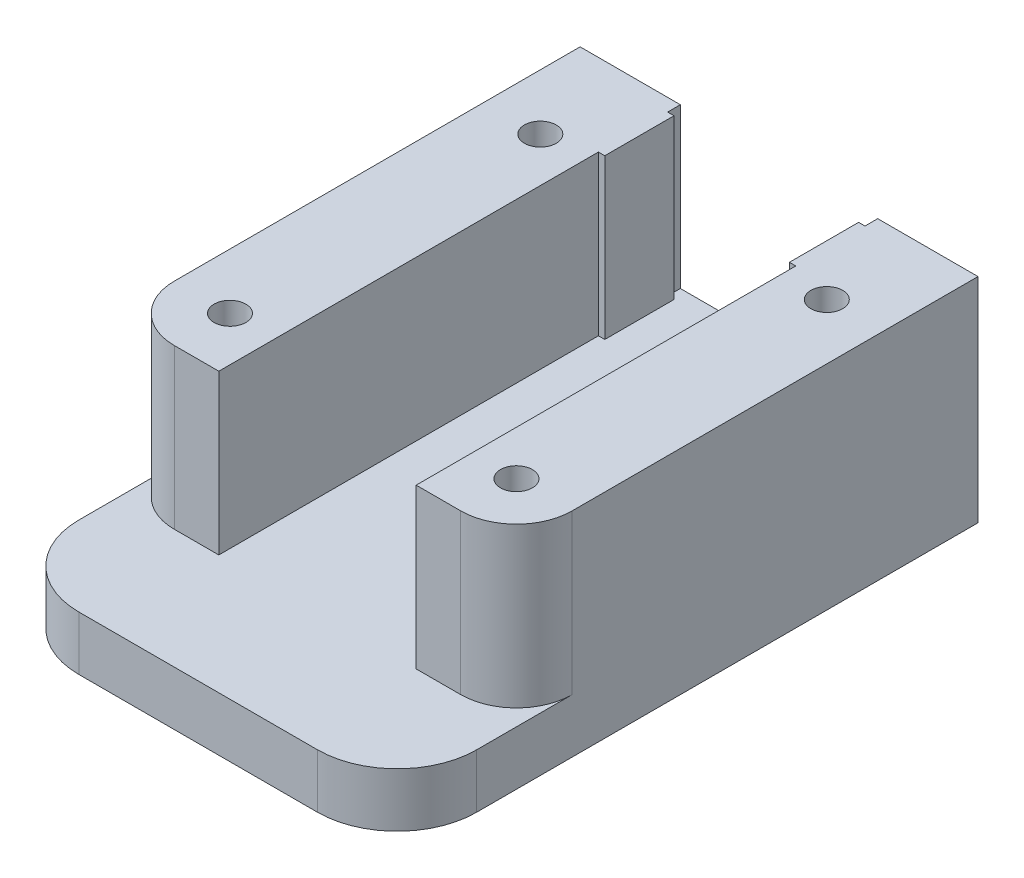
SolidWorks part; units mm, degrees
ref_plane "Front Plane" through (0, 0, 0) normal (0, 0, 1) x (1, 0, 0)
ref_plane "Top Plane" through (0, 0, 0) normal (0, 1, 0) x (1, 0, 0)
ref_plane "Right Plane" through (0, 0, 0) normal (1, 0, 0) x (0, 0, -1)
sketch "Sketch1" plane through (0, 0, 0) normal (0, 1, 0) x (1, 0, 0)
  line L1 (-15, -12.5) -> (15, -12.5)
  line L2 (-15, -12.5) -> (-15, 0)
  line L3 (-15, 0) -> (15, 0)
  line L4 (15, -12.5) -> (15, 0)
  line L5 (-15, -12.5) -> (15, 0) construction
  line L6 (-15, 0) -> (15, -12.5) construction
  point P0 (0, -6.25)
  dimension "D1" = 30
  dimension "D2" = 12.5
extrude "Boss-Extrude1" add sketch "Sketch1" along normal blind 1.6
sketch "Sketch2" plane through (0, 1.6, 0) normal (0, 1, 0) x (1, 0, 0)
  line L0 (15, 0) -> (-15, 0) construction
  line L1 (-12.5, -36.5) -> (12.5, -36.5)
  line L2 (-12.5, -36.5) -> (-12.5, 0)
  line L3 (-12.5, 0) -> (12.5, 0)
  line L4 (12.5, -36.5) -> (12.5, 0)
  line L5 (-12.5, -36.5) -> (12.5, 0) construction
  line L6 (-12.5, 0) -> (12.5, -36.5) construction
  line L7 (0, 0) -> (0, -18.25) construction
  line L8 (-15, -12.5) -> (15, -12.5) construction
  point P0 (0, -18.25)
  dimension "D1" = 25
  dimension "D2" = 24
extrude "Boss-Extrude2" add sketch "Sketch2" along normal blind 3.4
sketch "Sketch3" plane through (0, 5, 0) normal (0, 1, 0) x (1, 0, 0)
  line L1 (-12.5, 0) -> (-6.2, 0)
  line L2 (-12.5, 0) -> (-12.5, -30)
  line L3 (-12.5, -30) -> (-6.2, -30)
  line L4 (-6.2, 0) -> (-6.2, -30)
  line L6 (12.5, 0) -> (6.2, 0)
  line L7 (12.5, 0) -> (12.5, -30)
  line L8 (12.5, -30) -> (6.2, -30)
  line L9 (6.2, 0) -> (6.2, -30)
  dimension "D1" = 12.4
  dimension "D2" = 30
extrude "Boss-Extrude3" add sketch "Sketch3" along normal blind 10
fillet "Fillet1" radius 5 2 edges at (12.5, 3.3, 36.5) (-12.5, 3.3, 36.5)
sketch "Sketch4" plane through (0, 15, 0) normal (0, 1, 0) x (1, 0, 0)
  line L0 (-9, -25.5) -> (0, -25.5) construction
  line L1 (0, -25.5) -> (9, -25.5) construction
  circle A0 centre (-9, -25.5) radius 1
  circle A1 centre (9, -25.5) radius 1
  dimension "D3" = 2
  dimension "D1" = 18
  dimension "D2" = 25.5
extrude "Cut-Extrude1" cut sketch "Sketch4" against normal through all
sketch "Sketch5" plane through (0, 15, 0) normal (0, 1, 0) x (1, 0, 0)
  line L0 (-12.5, 0) -> (-12.5, -30) construction
  line L1 (-9, -29) -> (9, -29)
  line L2 (12.5, -30) -> (12.5, 0) construction
  line L3 (-12.5, -25.5) -> (-17.655, -25.5)
  line L4 (-17.655, -25.5) -> (-17.655, -35.3203)
  line L5 (-17.655, -35.3203) -> (17.216, -35.6292)
  line L6 (17.216, -35.6292) -> (17.216, -25.5)
  line L7 (17.216, -25.5) -> (12.5, -25.5)
  arc A0 (-12.5, -25.5) -> (-9, -29) centre (-9, -25.5) ccw
  arc A1 (9, -29) -> (12.5, -25.5) centre (9, -25.5) ccw
extrude "Cut-Extrude2" cut sketch "Sketch5" against normal up to surface (10 mm away) up to face at (0.305, 5, 27.2321)
sketch "Sketch9" plane through (0, 5, 0) normal (0, 1, 0) x (1, 0, 0)
  line L0 (-6.2, -29) -> (-6.2, 0) construction
  line L1 (-6.2, -0.8) -> (-5.8, -0.8)
  line L2 (-6.2, -0.8) -> (-6.2, -5.15)
  line L3 (-6.2, -5.15) -> (-5.8, -5.15)
  line L4 (-5.8, -0.8) -> (-5.8, -5.15)
  line L5 (6.2, 0) -> (6.2, -29) construction
  line L6 (6.2, -0.8) -> (5.8, -0.8)
  line L7 (6.2, -0.8) -> (6.2, -5.15)
  line L8 (6.2, -5.15) -> (5.8, -5.15)
  line L9 (5.8, -0.8) -> (5.8, -5.15)
  line L11 (6.2, 0) -> (-6.2, 0) construction
  point P14 (-5.2087, 0)
  dimension "D1" = 0.4
  dimension "D2" = 4.35
  dimension "D3" = 0.8
extrude "Boss-Extrude4" add sketch "Sketch9" along normal up to surface (10 mm away) up to face at (-9, 15, 26.5)
sketch "Sketch10" plane through (0, 15, 0) normal (0, 1, 0) x (1, 0, 0)
  line L0 (-9, -6) -> (-9, -25.5) construction
  line L1 (9, -6) -> (9, -25.5) construction
  line L2 (-6.2, 0) -> (-12.5, 0) construction
  circle A0 centre (-9, -6) radius 1
  circle A1 centre (9, -6) radius 1
  circle A3 centre (9, -25.5) radius 1 construction
  dimension "D1" = 6
extrude "Cut-Extrude3" cut sketch "Sketch10" against normal through all
sketch "Sketch11" plane through (0, 0, 0) normal (0, -1, 0) x (1, 0, 0)
  line L1 (-18.44, 14.8531) -> (17.776, 14.8531)
  line L2 (-18.44, 14.8531) -> (-18.44, -2.0545)
  line L3 (-18.44, -2.0545) -> (17.776, -2.0545)
  line L4 (17.776, 14.8531) -> (17.776, -2.0545)
extrude "Cut-Extrude4" cut sketch "Sketch11" against normal up to surface (1.6 mm away) up to face at (9, 1.6, 24.5)
